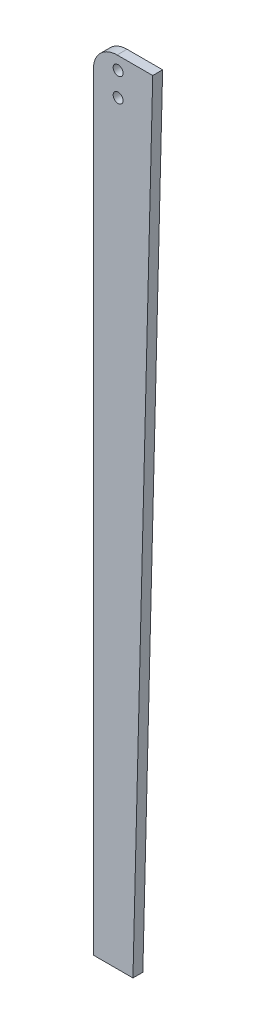
SolidWorks part; units mm, degrees
ref_plane "Front Plane" through (0, 0, 0) normal (0, 0, 1) x (1, 0, 0)
ref_plane "Top Plane" through (0, 0, 0) normal (0, 1, 0) x (1, 0, 0)
ref_plane "Right Plane" through (0, 0, 0) normal (1, 0, 0) x (0, 0, -1)
sketch "Sketch1" plane through (0, 0, 0) normal (0, 0, 1) x (1, 0, 0)
  line L0 (0, 0) -> (0, -7.62) construction
  line L1 (-0.3175, 4.1275) -> (11.1125, 4.1275)
  line L2 (-7.9375, -3.4925) -> (-7.9375, -249.8725)
  line L3 (-7.9375, -249.8725) -> (4.7625, -249.8725)
  line L4 (11.1125, 4.1275) -> (4.7625, -249.8725)
  circle A0 centre (0, 0) radius 1.5875
  circle A1 centre (0, -7.62) radius 1.5875
  arc A2 (-0.3175, 4.1275) -> (-7.9375, -3.4925) centre (-0.3175, -3.4925) ccw
  point P11 (-7.9375, 4.1275)
  dimension "D3" = 3.175
  dimension "D7" = 7.62
  dimension "D1" = 254
  dimension "D2" = 19.05
  dimension "D4" = 7.9375
  dimension "D5" = 4.1275
  dimension "D6" = 7.62
  dimension "D8" = 12.7
extrude "Boss-Extrude1" add sketch "Sketch1" along normal blind 3.175
